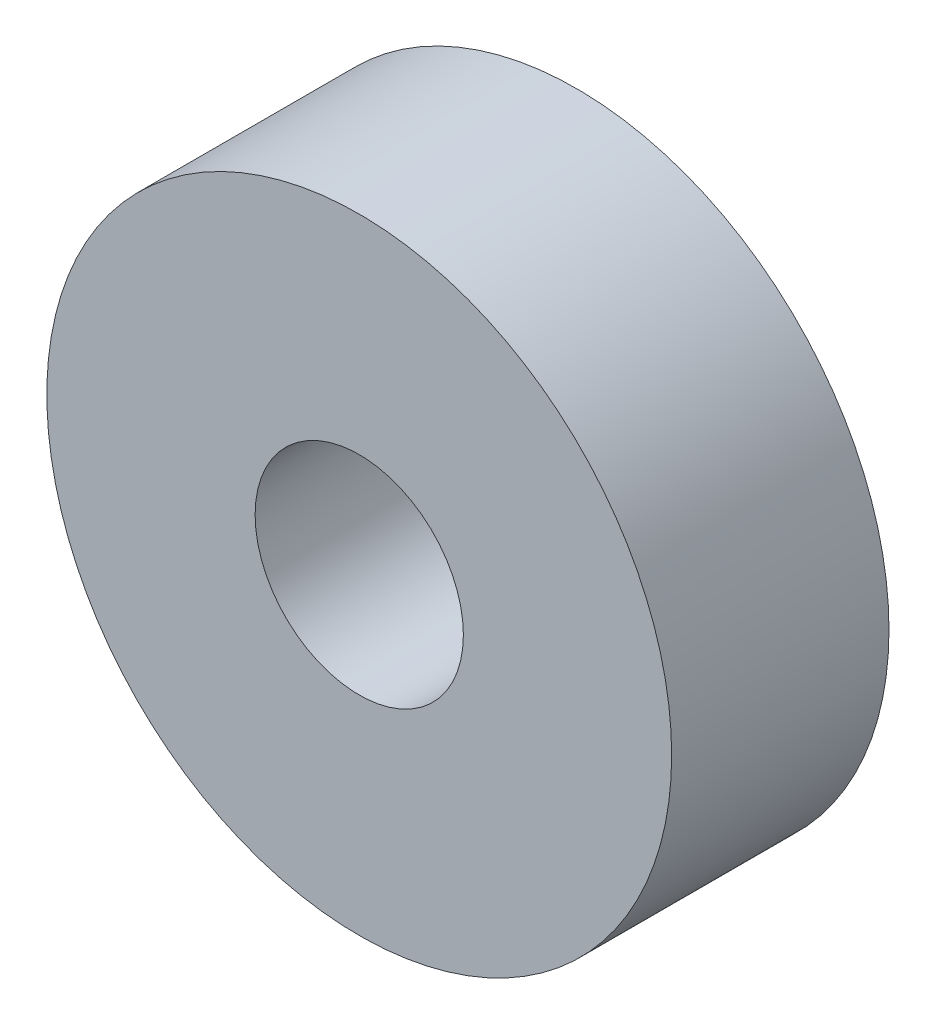
SolidWorks part; units mm, degrees
material "Acrylic (Medium-high impact)"
ref_plane "Front Plane" through (0, 0, 0) normal (0, 0, 1) x (1, 0, 0)
ref_plane "Top Plane" through (0, 0, 0) normal (0, 1, 0) x (1, 0, 0)
ref_plane "Right Plane" through (0, 0, 0) normal (1, 0, 0) x (0, 0, -1)
sketch "Sketch1" plane through (0, 0, 0) normal (0, 0, 1) x (1, 0, 0)
  circle A0 centre (0, 0) radius 1.4605
  circle A1 centre (0, 0) radius 4.3815
  dimension "D1" = 2.921
  dimension "D2" = 2.921
extrude "Boss-Extrude1" add sketch "Sketch1" along normal blind 3.048
